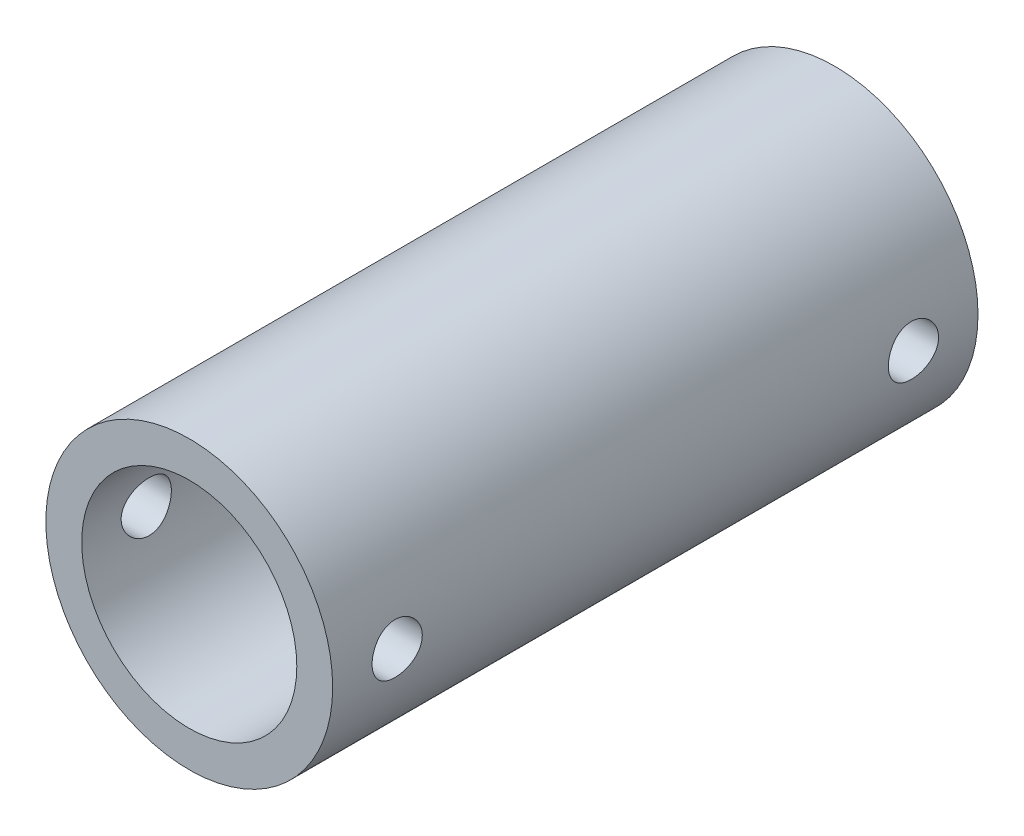
SolidWorks part; units mm, degrees
material "Plain Carbon Steel"
ref_plane "Front Plane" through (0, 0, 0) normal (0, 0, 1) x (1, 0, 0)
ref_plane "Top Plane" through (0, 0, 0) normal (0, 1, 0) x (1, 0, 0)
ref_plane "Right Plane" through (0, 0, 0) normal (1, 0, 0) x (0, 0, -1)
sketch "Sketch1" plane through (0, 0, 0) normal (0, 0, 1) x (1, 0, 0)
  circle A0 centre (0, 0) radius 30
  circle A1 centre (0, 0) radius 40
  dimension "D1" = 80
  dimension "D2" = 60
extrude "Boss-Extrude1" add sketch "Sketch1" along normal mid plane 180
sketch "Sketch2" plane through (0, 0, 0) normal (1, 0, 0) x (0, 0, -1)
  line L0 (0, 0) -> (-108.2882, 0) construction
  line L1 (0, 0) -> (0, -40) construction
  line L2 (-90, -40) -> (90, -40) construction
  line L3 (-90, 40) -> (-90, -40) construction
  circle A0 centre (-72, 0) radius 7
  circle A1 centre (72, 0) radius 7
  dimension "D1" = 14
  dimension "D2" = 18
extrude "Cut-Extrude1" cut sketch "Sketch2" against normal through all and the other way through all
